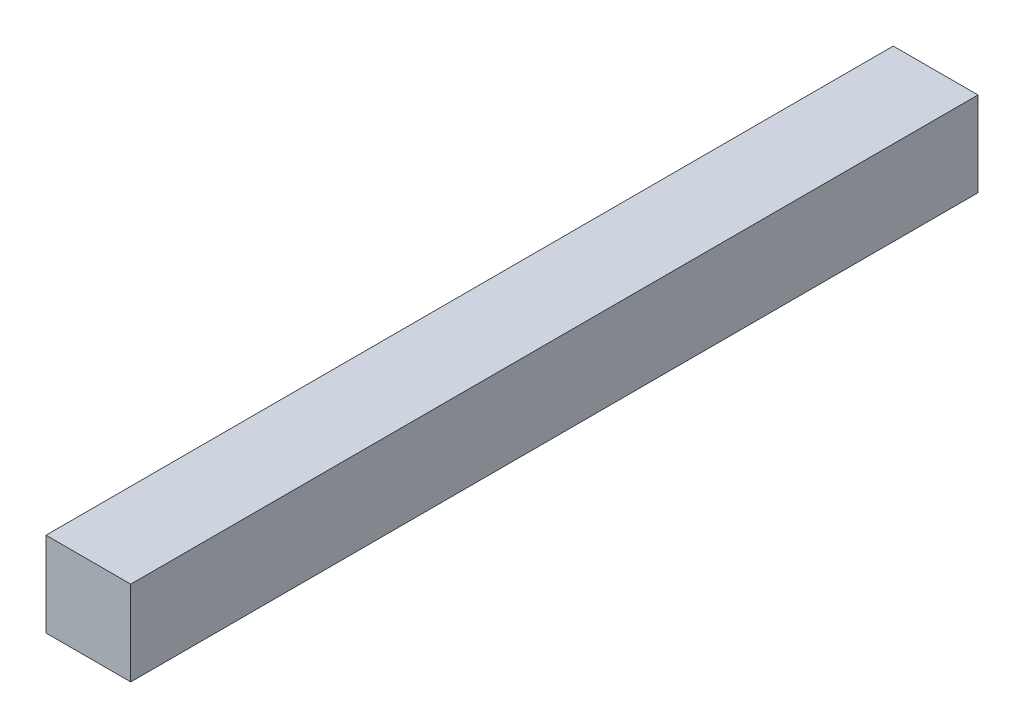
SolidWorks part; units mm, degrees
ref_plane "Front Plane" through (0, 0, 0) normal (0, 0, 1) x (1, 0, 0)
ref_plane "Top Plane" through (0, 0, 0) normal (0, 1, 0) x (1, 0, 0)
ref_plane "Right Plane" through (0, 0, 0) normal (1, 0, 0) x (0, 0, -1)
sketch "Sketch1" plane through (0, 0, 0) normal (0, 0, 1) x (1, 0, 0)
  line L1 (-15, 15) -> (15, 15)
  line L2 (-15, 15) -> (-15, -15)
  line L3 (-15, -15) -> (15, -15)
  line L4 (15, 15) -> (15, -15)
  line L5 (-15, 15) -> (15, -15) construction
  line L6 (-15, -15) -> (15, 15) construction
  point P0 (0, 0)
  dimension "D1" = 30
  dimension "D2" = 30
extrude "Boss-Extrude1" add sketch "Sketch1" along normal blind 300
sketch "Sketch2" plane through (0, -15, 0) normal (0, -1, 0) x (1, 0, 0)
  line L0 (-15, 300) -> (15, 300) construction
  line L1 (-15, 150) -> (15, 150) construction
  line L2 (-15, 300) -> (-15, 0) construction
  line L3 (15, 300) -> (15, 0) construction
  circle A0 centre (0, 280) radius 10
  dimension "D1" = 20
extrude "Cut-Extrude1" cut sketch "Sketch2" against normal blind 10
